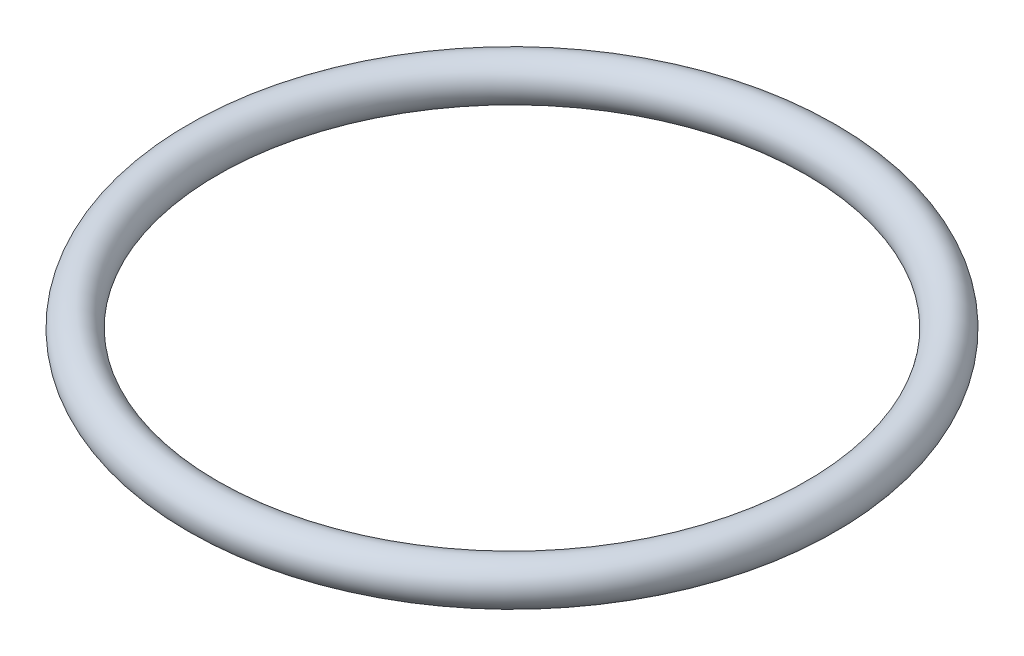
SolidWorks part; units mm, degrees
ref_plane "Front Plane" through (0, 0, 0) normal (0, 0, 1) x (1, 0, 0)
ref_plane "Top Plane" through (0, 0, 0) normal (0, 1, 0) x (1, 0, 0)
ref_plane "Right Plane" through (0, 0, 0) normal (1, 0, 0) x (0, 0, -1)
sketch "Sketch1" plane through (0, 0, 0) normal (0, 0, 1) x (1, 0, 0)
  line L0 (0, 52.0714) -> (0, -31.0714) construction
  circle A0 centre (-150, 0) radius 10
  dimension "D1" = 20
  dimension "D2" = 150
revolve "Revolve1" add sketch "Sketch1" angle 360 about L0
